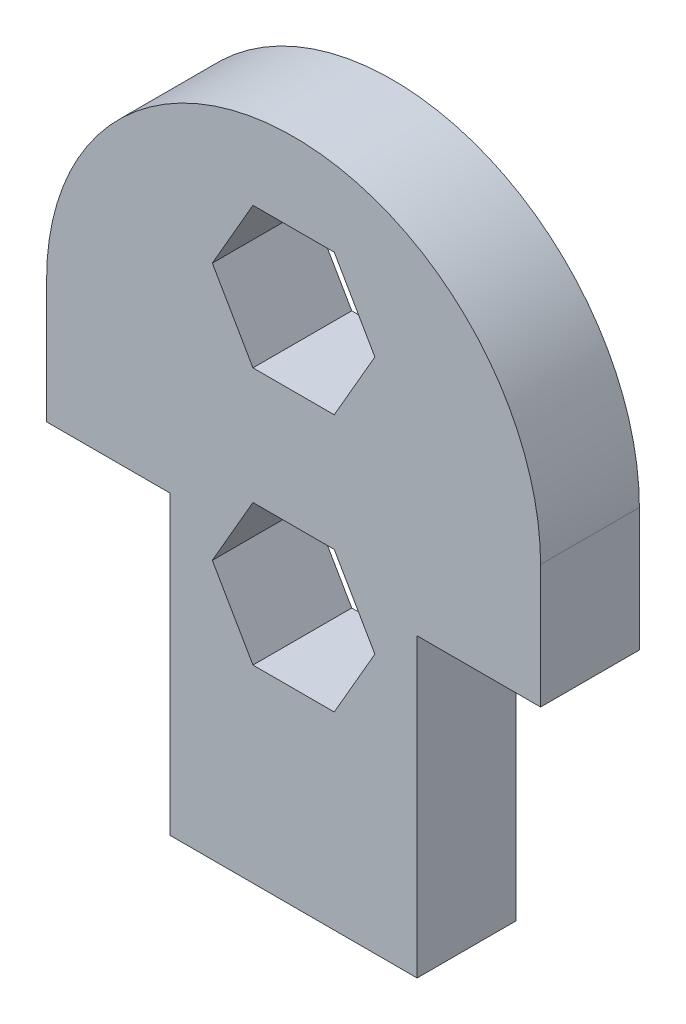
SolidWorks part; units mm, degrees
ref_plane "Front Plane" through (0, 0, 0) normal (0, 0, 1) x (1, 0, 0)
ref_plane "Top Plane" through (0, 0, 0) normal (0, 1, 0) x (1, 0, 0)
ref_plane "Right Plane" through (0, 0, 0) normal (1, 0, 0) x (0, 0, -1)
sketch "Sketch1" plane through (0, 0, 0) normal (0, 0, 1) x (1, 0, 0)
  line L0 (0, 0) -> (10, 0)
  line L1 (0, 0) -> (0, 4)
  line L2 (0, 4) -> (-2.5, 4)
  line L3 (3.3546, 18.0712) -> (6.6454, 18.0712)
  line L4 (-2.5, 4) -> (-2.5, 8)
  line L5 (-2.5, 8) -> (0, 8)
  line L6 (0, 8) -> (0, 12)
  line L7 (5, 0) -> (5, 27) construction
  line L8 (10, 0) -> (10, 4)
  line L9 (10, 4) -> (12.5, 4)
  line L10 (12.5, 4) -> (12.5, 8)
  line L11 (12.5, 8) -> (10, 8)
  line L12 (3.3546, 23.7712) -> (1.7091, 20.9212)
  line L13 (8.2909, 10.5) -> (6.6454, 13.35)
  line L14 (6.6454, 13.35) -> (3.3546, 13.35)
  line L15 (3.3546, 13.35) -> (1.7091, 10.5)
  line L16 (1.7091, 10.5) -> (3.3546, 7.65)
  line L17 (3.3546, 7.65) -> (6.6454, 7.65)
  line L18 (6.6454, 7.65) -> (8.2909, 10.5)
  line L19 (1.7091, 20.9212) -> (3.3546, 18.0712)
  line L20 (0, 12) -> (-5, 12)
  line L21 (10, 8) -> (10, 12)
  line L22 (6.6454, 18.0712) -> (8.2909, 20.9212)
  line L23 (8.2909, 20.9212) -> (6.6454, 23.7712)
  line L24 (6.6454, 23.7712) -> (3.3546, 23.7712)
  line L25 (10, 12) -> (15, 12)
  line L26 (-5, 12) -> (-5, 17)
  line L27 (15, 12) -> (15, 17)
  arc A1 (15, 17) -> (-5, 17) centre (5, 17) ccw
  dimension "D5" = 2.5
  dimension "D2" = 5.7
  dimension "D8" = 5
  dimension "D9" = 4
  dimension "D10" = 4
  dimension "D12" = 2.5
extrude "Boss-Extrude1" add sketch "Sketch1" along normal blind 4
sketch "Sketch2" plane through (0, 0, 4) normal (0, 0, 1) x (1, 0, 0)
  line L0 (-2.5, 8) -> (0, 8)
  line L1 (0, 8) -> (0, 4)
  line L2 (0, 4) -> (-2.5, 4)
  line L3 (-2.5, 4) -> (-2.5, 8)
  line L4 (10, 8) -> (12.5, 8)
  line L5 (12.5, 8) -> (12.5, 4)
  line L6 (12.5, 4) -> (10, 4)
  line L7 (10, 4) -> (10, 8)
extrude "Cut-Extrude1" cut sketch "Sketch2" against normal up to surface (4 mm away) up to face at (5, 20.9212, 0)
